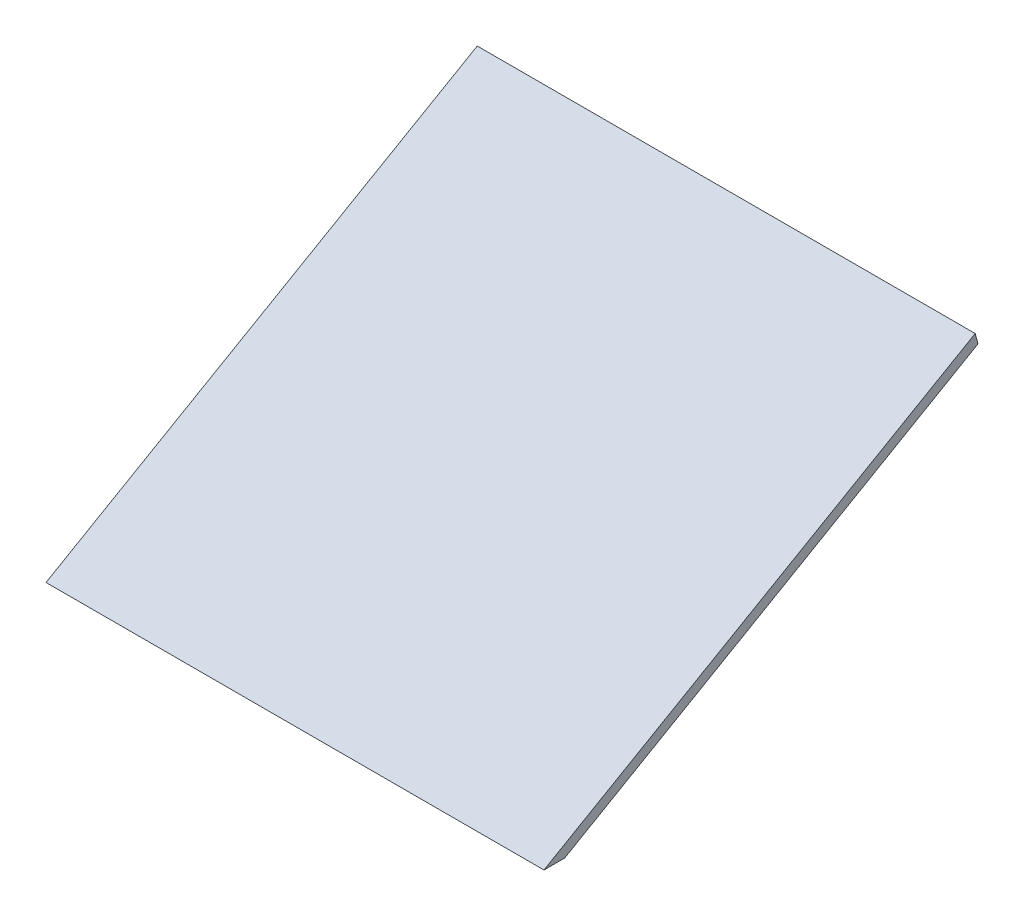
SolidWorks part; units mm, degrees
material "Pine"
ref_plane "Front Plane" through (0, 0, 0) normal (0, 0, 1) x (1, 0, 0)
ref_plane "Top Plane" through (0, 0, 0) normal (0, 1, 0) x (1, 0, 0)
ref_plane "Right Plane" through (0, 0, 0) normal (1, 0, 0) x (0, 0, -1)
sketch "Sketch1" plane through (0, 0, 0) normal (1, 0, 0) x (0, 0, -1)
  line L0 (0, 0) -> (25.4, 0)
  line L1 (25.4, 0) -> (531.332, 292.1)
  line L2 (531.332, 292.1) -> (527.9291, 304.8)
  line L3 (527.9291, 304.8) -> (0, 0)
  point P3 (530.132, 291.4071)
  dimension "D1" = 30
  dimension "D2" = 12.7
  dimension "D4" = 304.8
  dimension "D3" = 75
extrude "Boss-Extrude1" add sketch "Sketch1" along normal blind 609.6
equation "\"D3@Sketch1\"=(60+90)/2"
